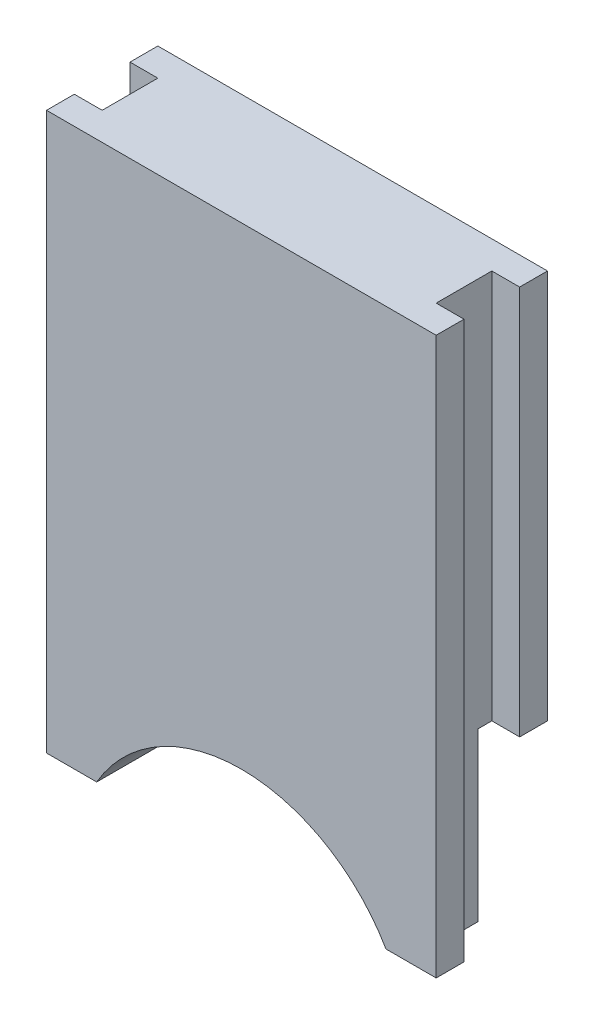
SolidWorks part; units mm, degrees
ref_plane "前视基准面" through (0, 0, 0) normal (0, 0, 1) x (1, 0, 0)
ref_plane "上视基准面" through (0, 0, 0) normal (0, 1, 0) x (1, 0, 0)
ref_plane "右视基准面" through (0, 0, 0) normal (1, 0, 0) x (0, 0, -1)
sketch "草图1" plane through (0, 0, 0) normal (0, 0, 1) x (1, 0, 0)
  line L0 (-14, 20) -> (0, 20)
  line L1 (-1.8038, 0) -> (0, 0)
  line L2 (-14, 0) -> (-12.1962, 0)
  line L3 (0, 0) -> (0, 20)
  line L4 (-14, 0) -> (-14, 20)
  line L5 (-1, 20) -> (-1, 0) construction
  line L6 (-13, 0) -> (-13, 20) construction
  line L7 (-13, 6) -> (-1, 6) construction
  line L8 (-14, 6) -> (-13, 6) construction
  line L9 (-1, 6) -> (0, 6) construction
  line L10 (-7, 0) -> (-7, 20) construction
  arc A0 (-1.8038, 0) -> (-12.1962, 0) centre (-7, -3) ccw
extrude "凸台-拉伸1" add sketch "草图1" along normal blind 4
sketch "草图2" plane through (0, 0, 0) normal (1, 0, 0) x (0, 0, -1)
  line L1 (-4, 0) -> (-4, 20) construction
  line L2 (0, 0) -> (-1.5, 0)
  line L3 (0, 0) -> (0, 6)
  line L4 (0, 6) -> (-1.5, 6)
  line L7 (-1.5, 0) -> (-1.5, 6)
  line L8 (-4, 20) -> (0, 20) construction
  dimension "D1" = 2.5
  dimension "D2" = 14
extrude "切除-拉伸1" cut sketch "草图2" against normal through all
sketch "草图3" plane through (0, 20, 0) normal (0, 1, 0) x (1, 0, 0)
  line L0 (-7, -4) -> (-7, 0) construction
  line L1 (0, -4) -> (-14, -4) construction
  line L2 (0, 0) -> (-14, 0) construction
  line L3 (-7, -2) -> (3.7572, -2) construction
  line L4 (0, -4) -> (0, 0) construction
  line L5 (0, -3) -> (-1, -3)
  line L6 (0, -3) -> (0, -1)
  line L7 (0, -1) -> (-1, -1)
  line L8 (-1, -3) -> (-1, -1)
  line L9 (-13, -3) -> (-13, -1)
  line L10 (-14, -1) -> (-13, -1)
  line L11 (-14, -3) -> (-14, -1)
  line L12 (-14, -3) -> (-13, -3)
  dimension "D1" = 2
  dimension "D2" = 12
extrude "切除-拉伸2" cut sketch "草图3" against normal through all and the other way through all
